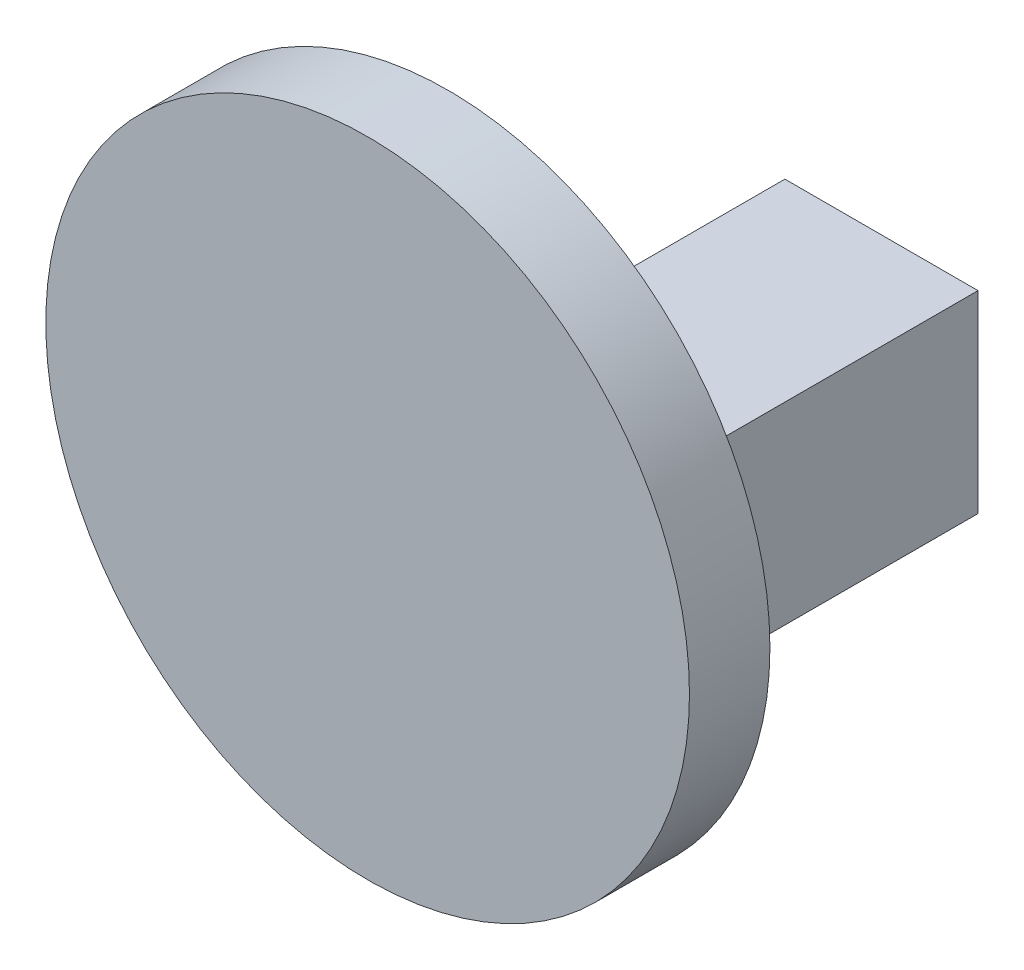
SolidWorks part; units mm, degrees
ref_plane "Front Plane" through (0, 0, 0) normal (0, 0, 1) x (1, 0, 0)
ref_plane "Top Plane" through (0, 0, 0) normal (0, 1, 0) x (1, 0, 0)
ref_plane "Right Plane" through (0, 0, 0) normal (1, 0, 0) x (0, 0, -1)
sketch "Sketch1" plane through (66.8982, 0, 0) normal (-1, 0, 0) x (0, 0, 1)
  line L4 (275.9813, 12.55) -> (275.9813, 0.55)
  line L7 (275.9813, 12.55) -> (254.5163, 12.55)
  line L9 (254.5163, 0.55) -> (252.3028, 0.55)
  line L10 (252.3028, 0.55) -> (252.3028, 12.55)
  line L11 (252.3028, 12.55) -> (254.5163, 12.55)
  line L12 (254.5163, 0.55) -> (275.9813, 0.55)
extrude "Boss-Extrude1" add sketch "Sketch1" along normal blind 5 and the other way blind 7
sketch "Sketch3" plane through (0, 0, 275.9813) normal (0, 0, 1) x (1, 0, 0)
  line L0 (61.8982, 12.55) -> (73.8982, 12.55) construction
  circle A0 centre (64.6471, 10.55) radius 20
  point P5 (67.8982, 12.55)
  dimension "D1" = 40
  dimension "D2" = 2
extrude "Boss-Extrude2" add sketch "Sketch3" along normal blind 5
fillet "Fillet1" radius 0.5 4 edges at (73.8982, 6.55, 275.9813) (67.8982, 0.55, 275.9813) (61.8982, 6.55, 275.9813) (67.8982, 12.55, 275.9813)
sketch "Sketch6" plane through (0, 0, 252.3028) normal (0, 0, -1) x (-1, 0, 0)
  circle A0 centre (-67.9692, 7.0134) radius 3.75
  dimension "D1" = 7.5
extrude "Cut-Extrude1" cut sketch "Sketch6" against normal blind 15
